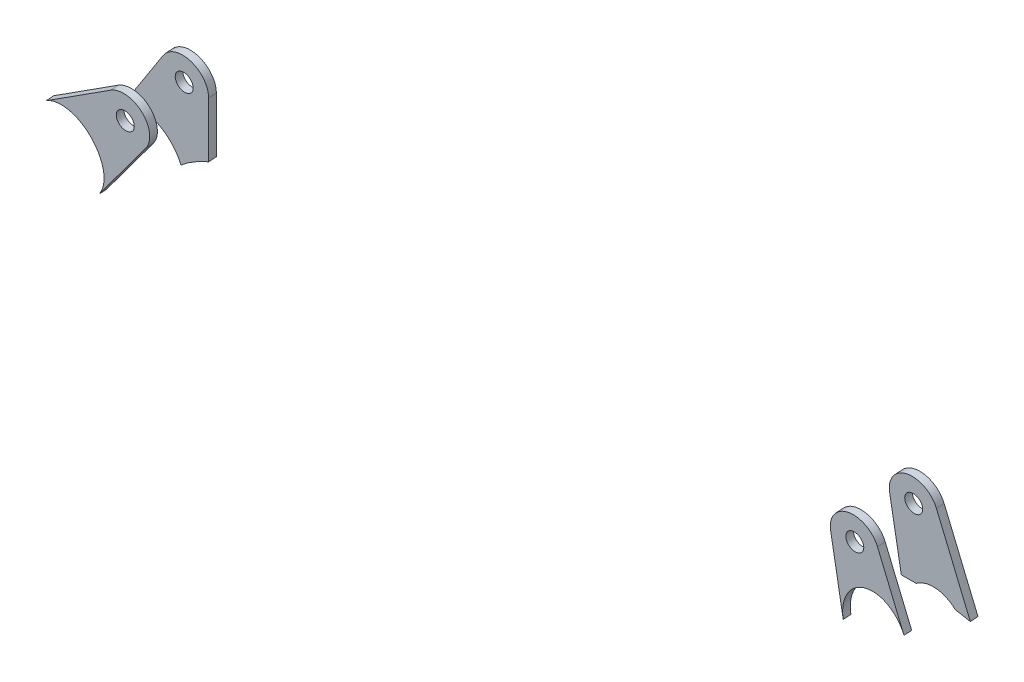
SolidWorks part; units mm, degrees
material "1.0545 (S355N)"
ref_plane "Płaszczyzna XY" through (0, 0, 0) normal (0, 0, 1) x (1, 0, 0)
ref_plane "Płaszczyzna XZ" through (0, 0, 0) normal (0, 1, 0) x (1, 0, 0)
ref_plane "Płaszczyzna YZ" through (0, 0, 0) normal (1, 0, 0) x (0, 0, -1)
ref_plane "Płaszczyzna1" through (0, -6.6268, 104.7678) normal (0, 0.0631, -0.998) x (-1, 0, 0)
ref_plane "Płaszczyzna2" through (0, -7.2581, 114.7478) normal (0, 0.0631, -0.998) x (-1, 0, 0)
sketch "Szkic1" plane through (0, -7.2581, 114.7478) normal (0, 0.0631, -0.998) x (-1, 0, 0)
  line L0 (-1189.7785, 265.076) -> (-1163.5599, 247.826)
  line L1 (-1202.5825, 251.4164) -> (-1182.7625, 225.1576)
  line L2 (-1488.0282, 260.0962) -> (-1496.6827, 233.6683)
  line L3 (-1469.5504, 256.1627) -> (-1472.5892, 226.7696)
  circle A0 centre (-1195, 257.1396) radius 3.5
  circle A1 centre (-1479, 257.1396) radius 3.5
  arc A2 (-1469.5504, 256.1627) -> (-1488.0282, 260.0962) centre (-1479, 257.1396) ccw
  arc A3 (-1189.7785, 265.076) -> (-1202.5825, 251.4164) centre (-1195, 257.1396) ccw
  circle A4 centre (-1195, 257.1396) radius 9.5 construction
  circle A5 centre (-1479, 257.1396) radius 9.5 construction
  spline S1 degree 3 poles (-1485, 213.9768) (-1510, 213.9768) (-1510, 243.0277) (-1485, 243.0277) (-1460, 243.0277) (-1460, 213.9768) (-1485, 213.9768) (-1510, 213.9768) (-1510, 243.0277) knots -0.5 0 0 0 0.5 0.5 0.5 1 1 1 1.5 1.5 1.5 weights 1 0.333333 0.333333 1 0.333333 0.333333 1 0.333333 0.333333 only from (-1485, 213.9768) to (-1485, 213.9768)
  spline S3 degree 3 poles (-1163.5242, 247.8025) (-1142.6959, 233.9757) (-1159.3489, 208.8901) (-1180.1772, 222.7168) (-1201.0055, 236.5436) (-1184.3526, 261.6293) (-1163.5242, 247.8025) (-1142.6959, 233.9757) (-1159.3489, 208.8901) knots -0.5 0 0 0 0.5 0.5 0.5 1 1 1 1.5 1.5 1.5 weights 1 0.333333 0.333333 1 0.333333 0.333333 1 0.333333 0.333333 only from (-1163.5242, 247.8025) to (-1163.5242, 247.8025)
  dimension "D1" = 7
  dimension "D2" = 6
extrude "Dodanie-wyciągnięcie1" add sketch "Szkic1" against normal blind 3 contours L2 S1 L3 A2 A1 | L1 S3 L0 A3 A0
ref_plane "Płaszczyzna3" through (0, -5.9955, 94.7877) normal (0, 0.0631, -0.998) x (-1, 0, 0)
sketch "Szkic2" plane through (0, -5.9955, 94.7877) normal (0, 0.0631, -0.998) x (-1, 0, 0)
  line L0 (-1204.4813, 256.5436) -> (-1203.0369, 233.5691)
  line L1 (-1187.087, 262.3965) -> (-1167.9798, 233.6349)
  line L2 (-1488.0282, 260.0962) -> (-1499.082, 226.3417)
  line L3 (-1469.5504, 256.1627) -> (-1472.378, 228.8126)
  line L4 (-1488.0282, 260.0962) -> (-1496.6827, 233.6683) construction
  line L5 (-1469.5504, 256.1627) -> (-1472.5892, 226.7696) construction
  circle A0 centre (-1479, 257.1396) radius 3.5 construction
  circle A1 centre (-1195, 257.1396) radius 3.5 construction
  circle A2 centre (-1479, 257.1396) radius 3.5
  circle A3 centre (-1195, 257.1396) radius 3.5
  arc A4 (-1469.5504, 256.1627) -> (-1488.0282, 260.0962) centre (-1479, 257.1396) ccw
  arc A5 (-1187.087, 262.3965) -> (-1204.4813, 256.5436) centre (-1195, 257.1396) ccw
  spline S1 degree 3 poles (-1499.082, 226.3417) (-1497.1645, 226.7255) (-1495.2498, 227.1069) (-1493.3384, 227.4859) knots 0.97807 0.97807 0.97807 0.97807 0.987766 0.987766 0.987766 0.987766 weights 0.974358 0.977963 0.981646 0.985405
  spline S3 degree 3 poles (-1478.2001, 228.8527) (-1476.2647, 228.8405) (-1474.3239, 228.8272) (-1472.378, 228.8126) knots 0.015706 0.015706 0.015706 0.015706 0.026884 0.026884 0.026884 0.026884 weights 0.970195 0.963236 0.956358 0.94956
  spline S5 degree 3 poles (-1493.3384, 227.4859) (-1488.9689, 232.0323) (-1483.1214, 232.5603) (-1478.2001, 228.8527) knots 0 0 0 0 1 1 1 1 weights 1 0.862952 0.862952 1
  spline S7 degree 3 poles (-1187.2736, 216.1393) (-1194.5084, 192.209) (-1245.4899, 207.6221) (-1238.2551, 231.5524) (-1231.0203, 255.4826) (-1180.0389, 240.0695) (-1187.2736, 216.1393) (-1194.5084, 192.209) (-1245.4899, 207.6221) knots -0.5 0 0 0 0.5 0.5 0.5 1 1 1 1.5 1.5 1.5 weights 1 0.333333 0.333333 1 0.333333 0.333333 1 0.333333 0.333333 only from (-1187.2736, 216.1393) to (-1187.2736, 216.1393)
  spline S9 degree 3 poles (-1191.8309, 226.5358) (-1186.1305, 244.4513) (-1169.2535, 246.0988) (-1166.1657, 229.041) (-1163.0778, 211.9833) (-1178.3469, 201.4536) (-1189.3857, 213.0282) knots 0 0 0 0 0.5 0.5 0.5 1 1 1 1 weights 1 0.506907 0.506907 1 0.506907 0.506907 1
  dimension "D3" = 6
  dimension "D1" = 6
  dimension "D2" = 30
extrude "Dodanie-wyciągnięcie2" add sketch "Szkic2" along normal blind 3 separate body contours S1 S5 S3 L3 A4 L2 A2 | S7 S9 L1 A5 L0 A3
